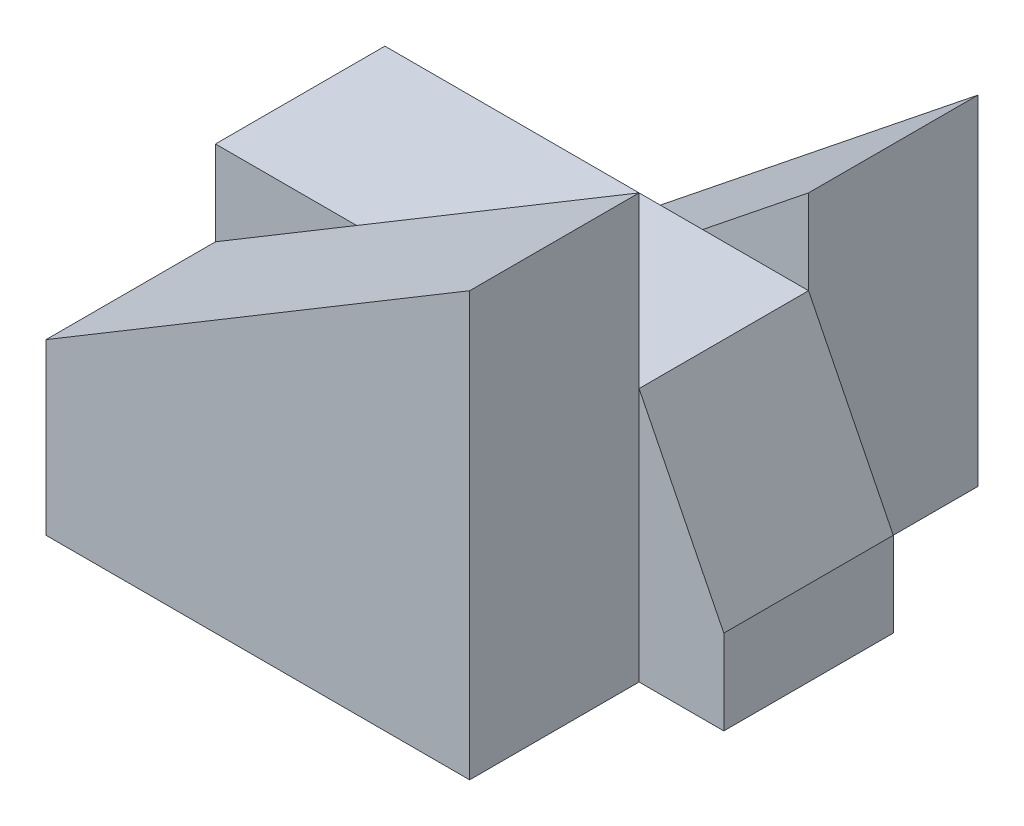
SolidWorks part; units mm, degrees
ref_plane "Front Plane" through (0, 0, 0) normal (0, 0, 1) x (1, 0, 0)
ref_plane "Top Plane" through (0, 0, 0) normal (0, 1, 0) x (1, 0, 0)
ref_plane "Right Plane" through (0, 0, 0) normal (1, 0, 0) x (0, 0, -1)
sketch "Sketch1" plane through (0, 0, 0) normal (0, 0, 1) x (1, 0, 0)
  line L0 (-25, 0) -> (0, 0)
  line L1 (0, 0) -> (0, 20)
  line L2 (0, 20) -> (-25, 0)
  dimension "D1" = 25
  dimension "D2" = 20
extrude "Boss-Extrude9" add sketch "Sketch1" along normal blind 10
sketch "Sketch7" plane through (0, 0, 10) normal (0, 0, 1) x (1, 0, 0)
  line L0 (-25, 0) -> (-25, 15)
  line L1 (-25, 15) -> (0, 15)
  line L2 (0, 15) -> (5, 5)
  line L3 (5, 5) -> (5, 0)
  line L4 (5, 0) -> (-25, 0)
  dimension "D1" = 15
  dimension "D2" = 25
  dimension "D3" = 30
  dimension "D4" = 5
extrude "Boss-Extrude10" add sketch "Sketch7" along normal blind 10
sketch "Sketch8" plane through (0, 0, 20) normal (0, 0, 1) x (1, 0, 0)
  line L1 (-25, 0) -> (0, 0)
  line L2 (-25, 0) -> (-25, 10)
  line L3 (-25, 10) -> (0, 10)
  line L4 (0, 0) -> (0, 10)
  dimension "D1" = 10
  dimension "D2" = 25
extrude "Boss-Extrude11" add sketch "Sketch8" along normal blind 10
sketch "Sketch9" plane through (0, 0, 20) normal (0, 0, 1) x (1, 0, 0)
  line L0 (-25, 10) -> (0, 25)
  line L1 (0, 25) -> (0, 10)
  line L2 (0, 10) -> (-25, 10) construction
  line L3 (0, 10) -> (-25, 10)
  line L4 (0, 0) -> (0, 10) construction
  dimension "D1" = 15
extrude "Boss-Extrude12" add sketch "Sketch9" along normal blind 10
